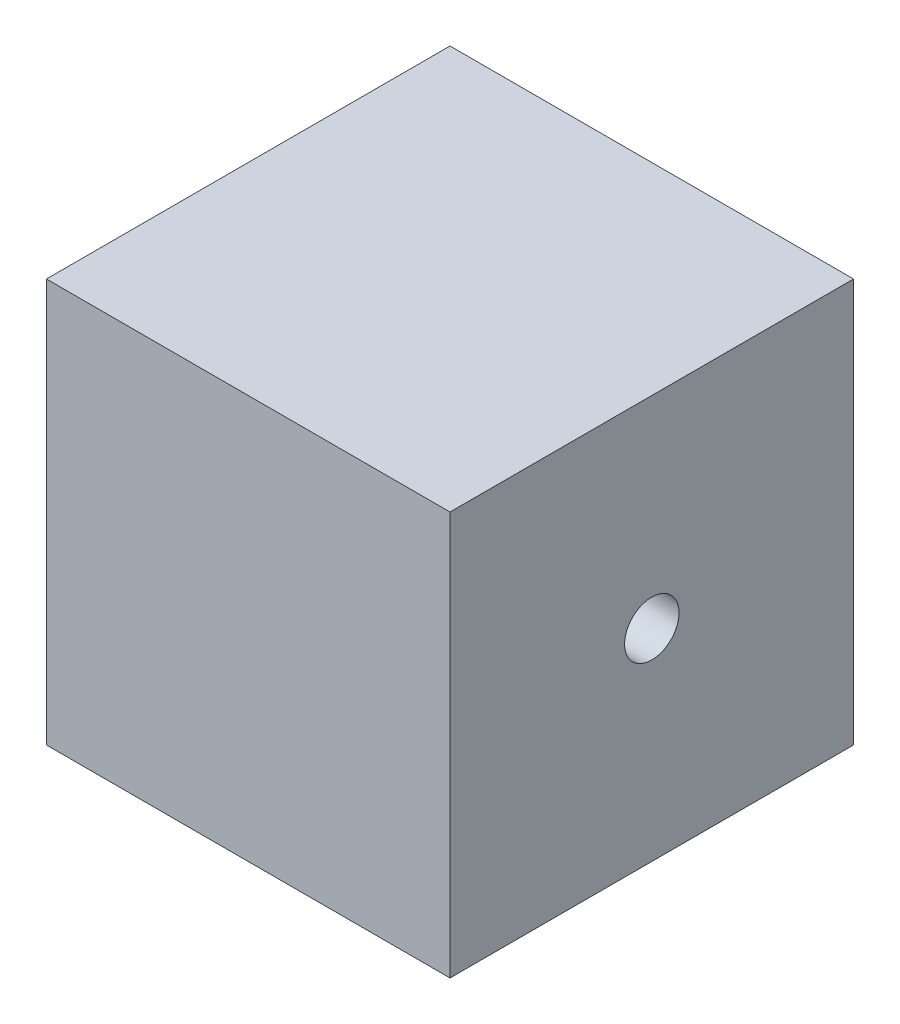
SolidWorks part; units mm, degrees
ref_plane "Front Plane" through (0, 0, 0) normal (0, 0, 1) x (1, 0, 0)
ref_plane "Top Plane" through (0, 0, 0) normal (0, 1, 0) x (1, 0, 0)
ref_plane "Right Plane" through (0, 0, 0) normal (1, 0, 0) x (0, 0, -1)
sketch "Sketch1" plane through (0, 0, 0) normal (0, 1, 0) x (1, 0, 0)
  line L1 (-10, 10) -> (10, 10)
  line L2 (-10, 10) -> (-10, -10)
  line L3 (-10, -10) -> (10, -10)
  line L4 (10, 10) -> (10, -10)
  line L5 (-10, 10) -> (10, -10) construction
  line L6 (-10, -10) -> (10, 10) construction
  point P0 (0, 0)
  dimension "D1" = 20
  dimension "D2" = 20
extrude "Boss-Extrude1" add sketch "Sketch1" along normal blind 20
sketch "Sketch2" plane through (10, 0, 0) normal (1, 0, 0) x (0, 0, -1)
  line L0 (0, 20) -> (0, 0) construction
  line L1 (-10, 20) -> (10, 20) construction
  line L2 (-10, 0) -> (10, 0) construction
  line L3 (-10, 10) -> (10, 10) construction
  line L4 (-10, 20) -> (-10, 0) construction
  line L5 (10, 20) -> (10, 0) construction
  circle A0 centre (0, 10) radius 1.3494
extrude "Cut-Extrude1" cut sketch "Sketch2" against normal blind 20
